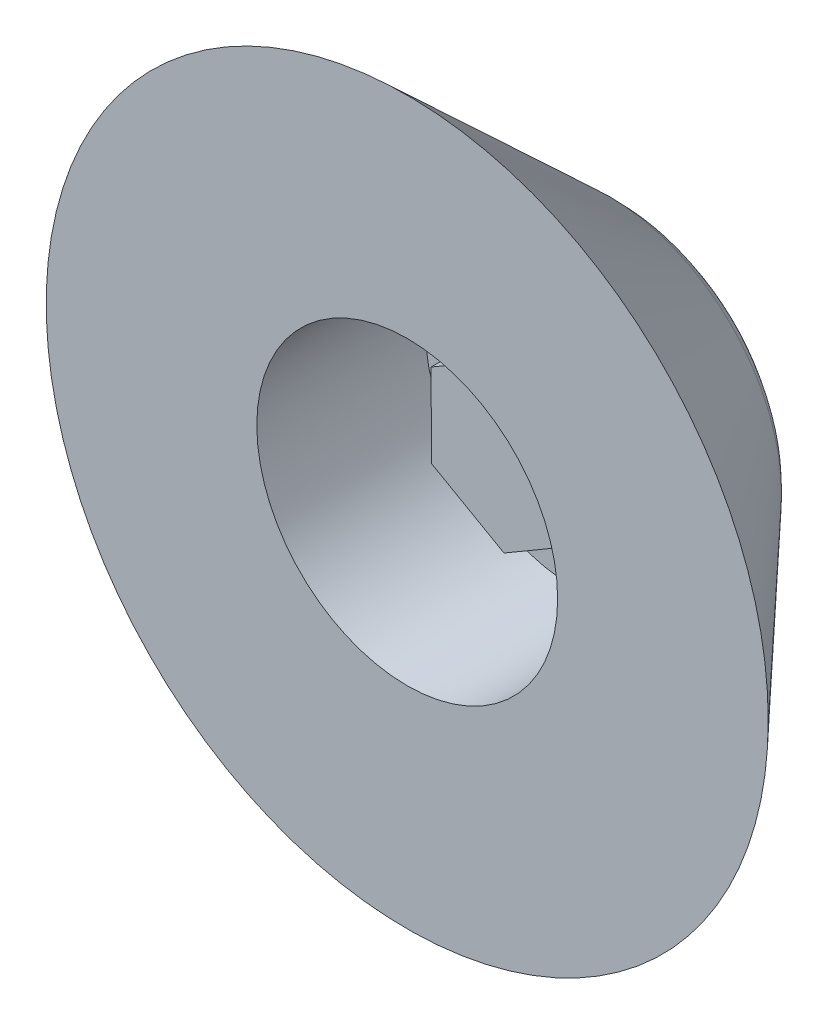
SolidWorks part; units mm, degrees
ref_plane "Front Plane" through (0, 0, 0) normal (0, 0, 1) x (1, 0, 0)
ref_plane "Top Plane" through (0, 0, 0) normal (0, 1, 0) x (1, 0, 0)
ref_plane "Right Plane" through (0, 0, 0) normal (1, 0, 0) x (0, 0, -1)
sketch "Sketch1" plane through (0, 0, 0) normal (0, 1, 0) x (1, 0, 0)
  line L0 (0, 0) -> (0, 10)
  line L1 (0, 10) -> (5.6593, 10)
  line L2 (5.6593, 10) -> (15, 0)
  line L3 (15, 0) -> (0, 0)
  dimension "D1" = 15
  dimension "D2" = 10
revolve "Revolve1" add sketch "Sketch1" angle 360 about L0
sketch "Sketch2" plane through (0, 0, 0) normal (0, 0, 1) x (1, 0, 0)
  line L1 (2.9895, 1.7502) -> (-0.021, 3.464)
  line L2 (-0.021, 3.464) -> (-3.0104, 1.7138)
  line L3 (-3.0104, 1.7138) -> (-2.9895, -1.7502)
  line L4 (-2.9895, -1.7502) -> (0.021, -3.464)
  line L5 (0.021, -3.464) -> (3.0104, -1.7138)
  line L6 (3.0104, -1.7138) -> (2.9895, 1.7502)
  circle A0 centre (0, 0) radius 3 construction
  circle A1 centre (0, 0) radius 6.25
  dimension "D2" = 12.5
  dimension "D1" = 6
extrude "Cut-Extrude1" cut sketch "Sketch2" against normal blind 7
sketch "Sketch4" plane through (0, 0, 0) normal (0, 0, 1) x (1, 0, 0)
  line L1 (-0.021, 3.464) -> (-3.0104, 1.7138)
  line L2 (-3.0104, 1.7138) -> (-2.9895, -1.7502)
  line L3 (-2.9895, -1.7502) -> (0.021, -3.464)
  line L4 (0.021, -3.464) -> (3.0104, -1.7138)
  line L5 (3.0104, -1.7138) -> (2.9895, 1.7502)
  line L6 (2.9895, 1.7502) -> (-0.021, 3.464)
  circle A0 centre (0, 0) radius 3 construction
extrude "Cut-Extrude2" cut sketch "Sketch4" against normal blind 4
fillet "Fillet1" radius 5 1 edges at (5.6593, 0, -10)
